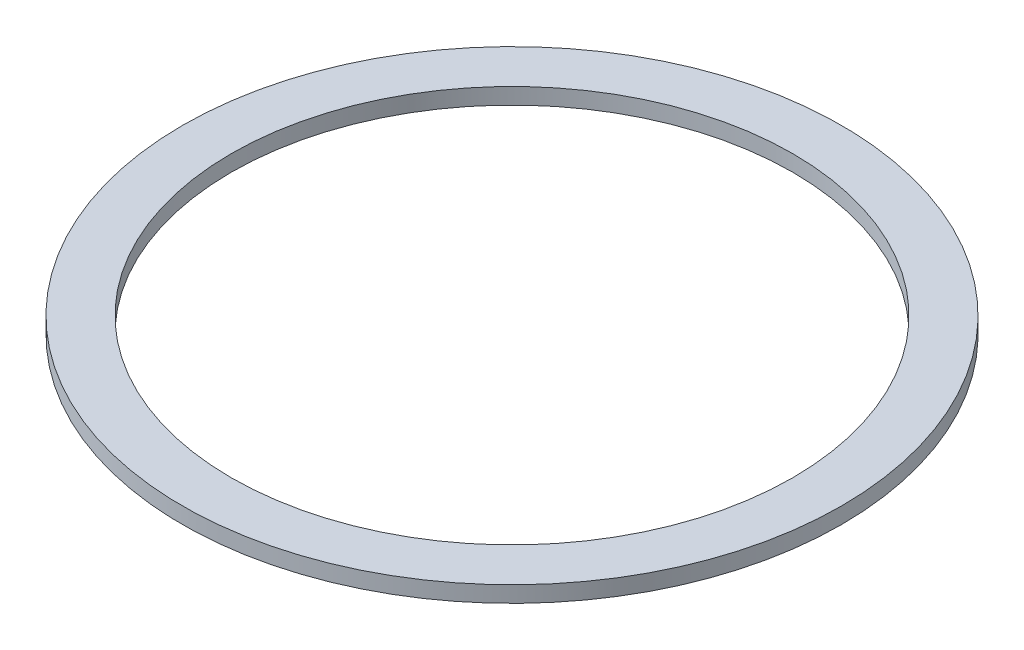
SolidWorks part; units mm, degrees
ref_plane "Front" through (0, 0, 0) normal (0, 0, 1) x (1, 0, 0)
ref_plane "Top" through (0, 0, 0) normal (0, 1, 0) x (1, 0, 0)
ref_plane "Right" through (0, 0, 0) normal (1, 0, 0) x (0, 0, -1)
sketch "Ring Base Profile" plane through (0, 0, 0) normal (0, 1, 0) x (1, 0, 0)
  circle A0 centre (0, 0) radius 70.375
  circle A2 centre (0, 0) radius 80.875
  dimension "D1" = 161.75
  dimension "D2" = 10.5
extrude "Ring Base Extrustion" add sketch "Ring Base Profile" along normal blind 1.5
sketch "Ring Lip Profile" plane through (0, 0, 0) normal (0, 0, 1) x (1, 0, 0)
  line L0 (-80.875, 1.5) -> (-80.875, -0.35)
  line L2 (-81.675, -2.5) -> (-81.675, 1.5)
  line L3 (-81.675, 1.5) -> (-80.875, 1.5)
  line L4 (-80.875, 0) -> (80.875, 0) construction
  line L5 (-80.875, -1.15) -> (-80.875, -2.5)
  line L6 (-80.875, 1.5) -> (-70.375, 1.5) construction
  line L7 (-70.375, 1.5) -> (-70.375, -2.5)
  line L8 (-81.675, -2.5) -> (-80.875, -2.5)
  line L9 (-69.575, -2.5) -> (-69.575, 1.5)
  line L10 (80.875, 1.5) -> (-80.875, 1.5) construction
  line L11 (-69.575, 1.5) -> (-70.375, 1.5)
  line L12 (-70.375, 1.5) -> (-70.375, -2.5) construction
  line L13 (-70.375, -2.5) -> (-69.575, -2.5) construction
  line L14 (-70.375, -2.5) -> (-69.575, -2.5)
  arc A0 (-80.875, -0.35) -> (-80.875, -1.15) centre (-80.875, -0.75) ccw
  dimension "D4" = 0.4
  dimension "D1" = 0.8
  dimension "D2" = 4
  dimension "D3" = 0.75
  dimension "D5" = 0.8
sweep "Ring Lip" add profiles "Ring Lip Profile" path edge at (0, 1.5, 80.875)
sketch "LED Channel Profile" plane through (0, 0, 0) normal (0, -1, 0) x (1, 0, 0)
  circle A0 centre (0, 0) radius 79.425
  circle A1 centre (0, 0) radius 81.675 construction
  circle A2 centre (0, 0) radius 71.825
  circle A3 centre (0, 0) radius 69.575 construction
  dimension "D1" = 2.25
  dimension "D2" = 2.25
extrude "LED Channel Cut" cut sketch "LED Channel Profile" against normal blind 0.75
